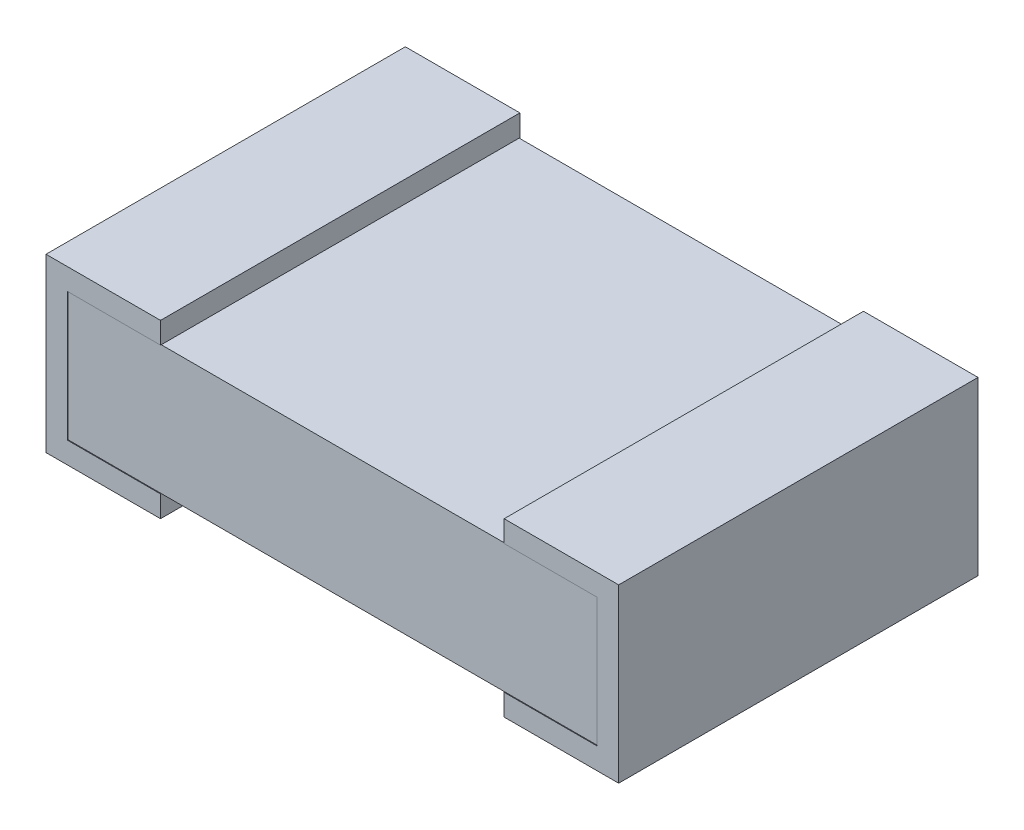
SolidWorks part; units mm, degrees
ref_plane "Front Plane" through (0, 0, 0) normal (0, 0, 1) x (1, 0, 0)
ref_plane "Top Plane" through (0, 0, 0) normal (0, 1, 0) x (1, 0, 0)
ref_plane "Right Plane" through (0, 0, 0) normal (1, 0, 0) x (0, 0, -1)
sketch "Sketch1" plane through (0, 0, 0) normal (0, 0, 1) x (1, 0, 0)
  line L0 (1.9558, 0.0762) -> (0.0762, 0.0762)
  line L1 (1.9558, 0.0762) -> (1.9558, 0.5334)
  line L2 (0.0762, 0.5334) -> (1.9558, 0.5334)
  line L3 (0.0762, 0.5334) -> (0.0762, 0.0762)
  dimension "D1" = 1.8796
  dimension "D2" = 0.4572
  dimension "D3" = 0.0762
  dimension "D4" = 0.0762
extrude "Base-Extrude" add sketch "Sketch1" against normal mid plane 1.27
ref_plane "Plane1" through (0, 0, -0.6375) normal (0, 0, -1) x (-1, 0, 0)
sketch "Sketch2" plane through (0, 0, -0.6375) normal (0, 0, -1) x (-1, 0, 0)
  line L0 (0, 0) -> (-0.4064, 0)
  line L1 (0, 0) -> (0, 0.6096)
  line L2 (0, 0.6096) -> (-0.4064, 0.6096)
  line L3 (-0.4064, 0.6096) -> (-0.4064, 0.5334)
  line L4 (-1.9558, 0.5334) -> (-0.0762, 0.5334) construction
  line L5 (-0.4064, 0) -> (-0.4064, 0.0762)
  line L6 (-0.0762, 0.0762) -> (-1.9558, 0.0762) construction
  line L7 (-0.0762, 0.5334) -> (-0.0762, 0.0762) construction
  line L8 (-0.0762, 0.0762) -> (-0.4064, 0.0762)
  line L9 (-0.4064, 0.5334) -> (-0.0762, 0.5334)
  line L10 (-0.0762, 0.5334) -> (-0.0762, 0.0762)
  dimension "D1" = 0.4064
  dimension "D2" = 0.4064
  dimension "D3" = 0.0762
extrude "Boss-Extrude1" add sketch "Sketch2" against normal blind 1.2751
ref_plane "Board Surface" through (1.016, 0, 0) normal (1, 0, 0) x (0, 0, -1)
mirror "Mirror1" about plane through (1.016, 0, 0) normal (1, 0, 0) of "Boss-Extrude1"
sketch "Component_Outline" plane through (0, 0, 0) normal (0, 1, 0) x (1, 0, 0)
  line L1 (0, 0.6375) -> (2.032, 0.6375)
  line L2 (0, 0.6375) -> (0, -0.6375)
  line L3 (0, -0.6375) -> (2.032, -0.6375)
  line L4 (2.032, 0.6375) -> (2.032, -0.6375)
